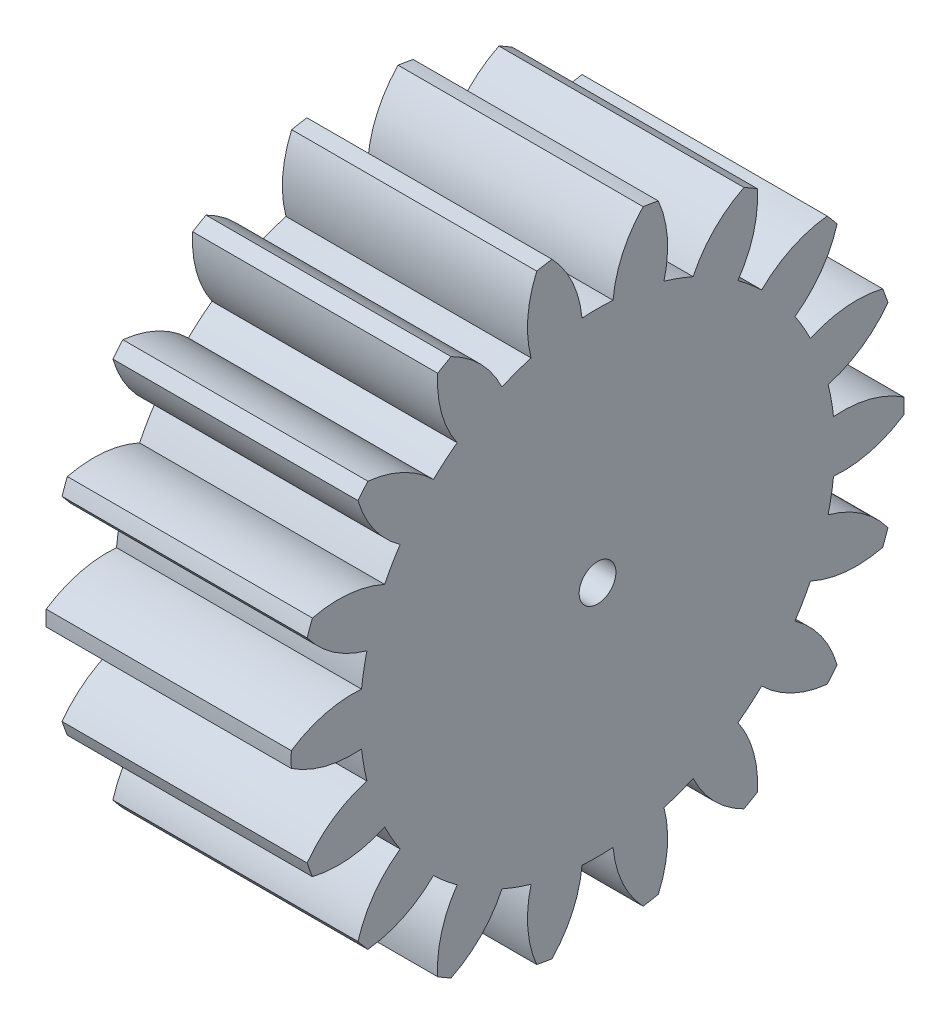
SolidWorks part; units mm, degrees
ref_plane "Plane1" through (0, 0, 0) normal (0, 0, 1) x (1, 0, 0)
ref_plane "Plane2" through (0, 0, 0) normal (0, 1, 0) x (1, 0, 0)
ref_plane "Plane3" through (0, 0, 0) normal (1, 0, 0) x (0, 0, -1)
sketch "HoldingSke" plane through (0, 0, 0) normal (0, 1, 0) x (1, 0, 0)
  line L0 (0, 0) -> (0.3804, -0.1236)
  line L1 (-15, 0) -> (100, 0) construction
  line L2 (0, 0) -> (-2.1039, 2.3779)
  line L3 (0, 0) -> (-11.863, 4.5341)
  line L4 (0, 0) -> (8.2133, 2.6687)
  line L5 (0, 0) -> (-46.8476, -17.4728)
  line L6 (0, 0) -> (-16.5793, -11.1861)
  line L7 (-2.1039, 2.3779) -> (8.6586, 51.2059)
  line L8 (-76.2, 54.61) -> (-75.7, 54.61)
  line L9 (-71.009, 38.7566) -> (-53.1078, 45.2721)
  line L10 (-76.2, 71.12) -> (104.1128, 71.12)
  line L11 (0, 0) -> (-20, 0)
  line L12 (-76.2, 101.6) -> (-76.113, 101.6)
  line L13 (24.9733, 27.94) -> (52.9518, 28.4284)
  line L14 (24.9733, 27.94) -> (24.9743, 27.94)
  line L15 (24.9733, 27.94) -> (100.4006, 29.5858)
  line L16 (-63.627, -2.5) -> (-12.827, -2.5)
  circle A0 centre (0, 0) radius 1.5
  circle A1 centre (0, 0) radius 19.374
  circle A2 centre (0, 0) radius 37.5
  circle A3 centre (0, 0) radius 1.5
  dimension "MHD" = 38.748
  dimension "Hub_dia" = 75
  dimension "Bore" = 3
  dimension "MBD" = 3
  dimension "Num_teeth" = 18
  dimension "Pitch" = 0.4
  dimension "Overall_len" = 50
  dimension "Show_teeth" = 18
  dimension "Thickness" = 20
  dimension "OAL" = 50.0001
  dimension "T_dim" = 0.5
  dimension "Ap" = 20
  dimension "H" = 19.05
  dimension "Pitch_radius" = 180.3128
  dimension "Width" = 20
  dimension "Backlash" = 0.087
  dimension "Addendum_fac" = 1
  dimension "Dedendum_fac" = 1.25
  dimension "Clearance_fac" = 0.25
  dimension "Dedendum_add" = 0.001
  dimension "Module" = 2.5
sketch "BasProSke" plane through (0, 0, 0) normal (0, 1, 0) x (1, 0, 0)
  line L0 (-10, 0) -> (60, 0) construction
  line L1 (0, 0) -> (0, 25)
  line L2 (0, 0) -> (20, 0)
  line L3 (20, 0) -> (20, 25)
  line L4 (20, 25) -> (0, 25)
  dimension "Thickness" = 20
  dimension "Diameter" = 50
revolve "Base-Revolve" add sketch "BasProSke" angle 360 about L0
sketch "TooCutSke" plane through (0, 0, 0) normal (1, 0, 0) x (0, 0, -1)
  line L1 (0, 0) -> (0, 107) construction
  line L2 (0, 0) -> (-2.1132, 22.4005) construction
  line L3 (0, 0) -> (-7.7889, 44.1729) construction
  line L4 (-2.1132, 22.4005) -> (-3.8944, 22.0865) construction
  arc A0 (1.2647, 19.3327) -> (-1.2647, 19.3327) centre (0, 0) ccw
  arc A1 (3.7401, 24.7443) -> (-3.7401, 24.7443) centre (0, 0) ccw
  circle A2 centre (0, 0) radius 22.5 construction
  circle A3 centre (0, 0) radius 21.1431 construction
  arc A4 (-1.2647, 19.3327) -> (-3.7401, 24.7443) centre (-10.2266, 18.5053) ccw
  arc A5 (3.7401, 24.7443) -> (1.2647, 19.3327) centre (10.2266, 18.5053) ccw
  dimension "Root_dia" = 38.748
  dimension "Overcut_dia" = 50.0508
  dimension "Pitch_dia" = 45
  dimension "Base_dia" = 42.2862
  dimension "Flank_rad" = 9
  dimension "Half_ang" = 10
  dimension "Half_CT" = 1.8088
extrude "ToothCut" cut sketch "TooCutSke" along normal through all
fillet "Breaks" [suppressed] radius 0.05
fillet "RootFillets" [suppressed] radius 0.626
pattern_circular "TeethCuts" count 18 every 20 about axis through (-10, 0, 0) along (1, 0, 0) of "ToothCut", "RootFillets", "Breaks"
sketch "HubNeaOneSke" plane through (0, 0, 0) normal (-1, 0, 0) x (0, 0, 1)
  circle A0 centre (0, 0) radius 19.374
  dimension "Diameter" = 38.748
extrude "HubNearOne" [suppressed] add sketch "HubNeaOneSke" along normal blind 30.0001
sketch "HubNeaBotSke" plane through (0, 0, 0) normal (-1, 0, 0) x (0, 0, 1)
  circle A0 centre (0, 0) radius 19.374
  dimension "Diameter" = 38.748
extrude "HubNearBoth" [suppressed] add sketch "HubNeaBotSke" along normal blind 15
ref_plane "FarPln" through (20, 0, 0) normal (1, 0, 0) x (0, 0, -1)
sketch "HubFarSke" plane through (20, 0, 0) normal (1, 0, 0) x (0, 0, -1)
  circle A0 centre (0, 0) radius 19.374
  dimension "Diameter" = 38.748
extrude "HubFar" [suppressed] add sketch "HubFarSke" along normal blind 15
sketch "BorSke" plane through (0, 0, 0) normal (1, 0, 0) x (0, 0, -1)
  circle A0 centre (0, 0) radius 1.5
  dimension "Diameter" = 3
extrude "Bore" cut sketch "BorSke" along normal mid plane 100.0001
sketch "KeySke" plane through (0, 0, 0) normal (1, 0, 0) x (0, 0, -1)
  line L0 (-0.6, 0) -> (-0.6, 2)
  line L1 (-0.6, 2) -> (0.6, 2)
  line L2 (0.6, 2) -> (0.6, 0)
  line L3 (0, 0) -> (0, 34) construction
  line L4 (-0.6, 0) -> (0.6, 0)
  dimension "Offset" = 2
  dimension "Width" = 1.2
extrude "Keyway" [suppressed] cut sketch "KeySke" along normal mid plane 100.0001
pattern_circular "Keyway2" [suppressed] count 2 every 90 about axis through (-10, 0, 0) along (1, 0, 0)
equation "' \"Module@HoldingSke\" = 6.35"
equation "' \"Num_teeth@HoldingSke\" = 12"
equation "' \"Ap@HoldingSke\" =  20"
equation "' \"Ap@HoldingSke\" = 20"
equation "' \"Width@HoldingSke\" = 0.5 * 25.4"
equation "' \"Hub_dia@HoldingSke\"= 1 * 25.4"
equation "' \"Hub_dia@HoldingSke\" = 1 * 25.4"
equation "' \"Overall_len@HoldingSke\" = 1.0 * 25.4"
equation "' \"Bore@HoldingSke\" = 0.75 * 25.4"
equation "' \"T_dim@HoldingSke\" = 0.1 * 25.4"
equation "' \"Width@KeySke\" = 0.25 * 25.4"
equation "' \"Show_teeth@HoldingSke\" = 13"
equation "' \"Backlash@HoldingSke\" = 0.009 * 25.4"
equation "' \"Addendum_fac@HoldingSke\" = 1.0"
equation "' \"Dedendum_fac@HoldingSke\" = 1.25"
equation "' \"Dedendum_add@HoldingSke\" = 0.00005 * 25.4"
equation "' \"Clearance_fac@HoldingSke\" = 0.25"
equation "\"Pitch@HoldingSke\" = 1 / \"Module@HoldingSke\""
equation "\"Overcut_dia@TooCutSke\" = (\"Num_teeth@HoldingSke\" + 2 * \"Addendum_fac@HoldingSke\") / \"Pitch@HoldingSke\" + 0.002 * 25.4"
equation "\"Pitch_dia@TooCutSke\" = \"Num_teeth@HoldingSke\" / \"Pitch@HoldingSke\""
equation "\"Base_dia@TooCutSke\" = \"Num_teeth@HoldingSke\" / \"Pitch@HoldingSke\" * cos((\"Ap@HoldingSke\"  * 3.14159265 / 180))"
equation "\"Root_dia@TooCutSke\" = (\"Num_teeth@HoldingSke\" + 2) / \"Pitch@HoldingSke\" - 2 * (\"Addendum_fac@HoldingSke\" + \"Dedendum_fac@HoldingSke\") / \"Pitch@HoldingSke\" - \"Dedendum_add@HoldingSke\" * 2"
equation "\"Half_ang@TooCutSke\" = 180 / \"Num_teeth@HoldingSke\""
equation "\"Half_CT@TooCutSke\" = \"Num_teeth@HoldingSke\" / \"Pitch@HoldingSke\" * sin((3.14159265 / 2 / \"Num_teeth@HoldingSke\")) / 2 - 7 * \"Backlash@HoldingSke\" / 4"
equation "\"Flank_rad@TooCutSke\" = \"Num_teeth@HoldingSke\" / \"Pitch@HoldingSke\" / 5"
equation "\"Radius@RootFillets\" = \"Clearance_fac@HoldingSke\" / \"Pitch@HoldingSke\" + \"Dedendum_add@HoldingSke\""
equation "\"Break_rad@Breaks\" = 0.02 / \"Pitch@HoldingSke\""
equation "\"Thickness@HoldingSke\" = \"Width@HoldingSke\""
equation "\"OAL@HoldingSke\" = \"Thickness@HoldingSke\""
equation "\"MHD@HoldingSke\" = (\"Num_teeth@HoldingSke\" + 2) / \"Pitch@HoldingSke\" - 2 * (\"Addendum_fac@HoldingSke\" + \"Dedendum_fac@HoldingSke\")  / \"Pitch@HoldingSke\" - \"Dedendum_add@HoldingSke\" * 2"
equation "\"MBD@HoldingSke\" = (\"Num_teeth@HoldingSke\" + 2) / \"Pitch@HoldingSke\" - 2 * (\"Addendum_fac@HoldingSke\" + \"Dedendum_fac@HoldingSke\")  / \"Pitch@HoldingSke\" - \"Dedendum_add@HoldingSke\" * 2 - 0.002 * 25.4"
equation "\"MHD@HoldingSke\" = ((sgn( \"MHD@HoldingSke\" - \"Hub_dia@HoldingSke\" )-1)*( \"MHD@HoldingSke\" - \"Hub_dia@HoldingSke\" ))/-2+ \"Hub_dia@HoldingSke\""
equation "\"MBD@HoldingSke\" = ((sgn( \"MBD@HoldingSke\" - \"Bore@HoldingSke\" )-1)*( \"MBD@HoldingSke\" - \"Bore@HoldingSke\" ))/-2+ \"Bore@HoldingSke\""
equation "\"OAL@HoldingSke\" = ((sgn( \"OAL@HoldingSke\" - \"Overall_len@HoldingSke\" )+1)*( \"OAL@HoldingSke\" - \"Overall_len@HoldingSke\" ))/2 + \"Overall_len@HoldingSke\" + 0.000002 * 25.4"
equation "\"Num_teeth@TeethCuts\" = int( \"Show_teeth@HoldingSke\" ) + 1"
equation "\"Num_teeth@TeethCuts\" = ((sgn( \"Num_teeth@TeethCuts\" - \"Num_teeth@HoldingSke\" )-1)*( \"Num_teeth@TeethCuts\" - \"Num_teeth@HoldingSke\" ))/-2+ \"Num_teeth@HoldingSke\""
equation "\"Num_teeth@TeethCuts\" = ((sgn( \"Num_teeth@TeethCuts\" - 2.0)+1)*( \"Num_teeth@TeethCuts\" - 2.0))/2 +2.0"
equation "\"Angle@TeethCuts\" = 360.0 / \"Num_teeth@HoldingSke\""
equation "\"Diameter@BasProSke\" = (\"Num_teeth@HoldingSke\" + 2 * \"Addendum_fac@HoldingSke\") / \"Pitch@HoldingSke\""
equation "\"Thickness@BasProSke\"  = \"Thickness@HoldingSke\""
equation "' \"Fillet_rad@BasProSke\" =  \"Thickness@HoldingSke\" * 0.05"
equation "' \"Fillet_rad@BasProSke\" = \"Thickness@HoldingSke\" * 0.05"
equation "\"MHD@HoldingSke\" = ((sgn( \"MHD@HoldingSke\" - \"Root_dia@TooCutSke\" )-1)*( \"MHD@HoldingSke\" - \"Root_dia@TooCutSke\" ))/-2+ \"Root_dia@TooCutSke\""
equation "\"Diameter@HubNeaOneSke\" = \"MHD@HoldingSke\""
equation "\"Length@HubNearOne\" = \"OAL@HoldingSke\" - \"Thickness@BasProSke\""
equation "\"Diameter@HubNeaBotSke\" = \"MHD@HoldingSke\""
equation "\"Length@HubNearBoth\" = ( \"OAL@HoldingSke\" - \"Thickness@BasProSke\" ) / 2.0"
equation "\"Thickness@FarPln\" = \"Thickness@BasProSke\""
equation "\"Diameter@HubFarSke\" = \"MHD@HoldingSke\""
equation "\"Length@HubFar\" = ( \"OAL@HoldingSke\" - \"Thickness@BasProSke\" ) / 2.0"
equation "\"Diameter@BorSke\" = \"MBD@HoldingSke\""
equation "\"D1@Bore\" = \"OAL@HoldingSke\" * 2.0"
equation "\"D1@Keyway\" = \"OAL@HoldingSke\" * 2.0"
equation "\"Offset@KeySke\" = \"T_dim@HoldingSke\" + \"MBD@HoldingSke\" / 2.0"
